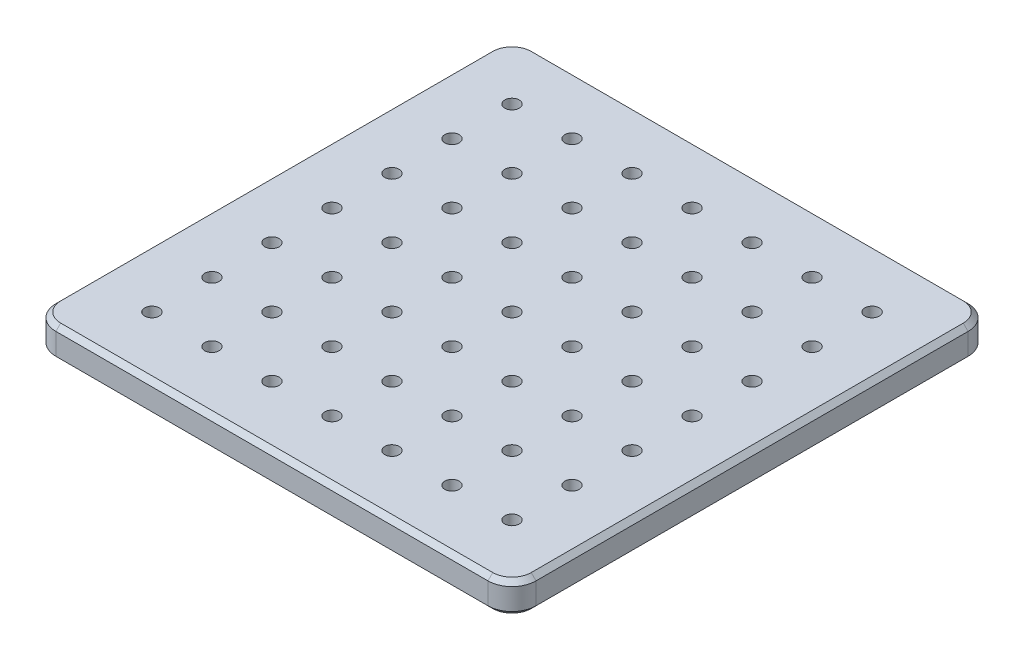
SolidWorks part; units mm, degrees
material "铸造合金钢"
ref_plane "前视基准面" through (0, 0, 0) normal (0, 0, 1) x (1, 0, 0)
ref_plane "上视基准面" through (0, 0, 0) normal (0, 1, 0) x (1, 0, 0)
ref_plane "右视基准面" through (0, 0, 0) normal (1, 0, 0) x (0, 0, -1)
sketch "草图1" plane through (0, 0, 0) normal (0, 1, 0) x (1, 0, 0)
  line L1 (-90, 100) -> (90, 100)
  line L2 (-100, 90) -> (-100, -90)
  line L3 (-90, -100) -> (90, -100)
  line L4 (100, 90) -> (100, -90)
  line L5 (-100, 100) -> (100, -100) construction
  line L6 (-100, -100) -> (100, 100) construction
  arc A0 (-90, 100) -> (-100, 90) centre (-90, 90) ccw
  arc A1 (90, 100) -> (100, 90) centre (90, 90) cw
  arc A2 (90, -100) -> (100, -90) centre (90, -90) ccw
  arc A3 (-100, -90) -> (-90, -100) centre (-90, -90) ccw
  circle A4 centre (-75, 75) radius 3
  circle A5 centre (-50, 75) radius 3
  circle A6 centre (-25, 75) radius 3
  circle A7 centre (0, 75) radius 3
  circle A8 centre (25, 75) radius 3
  circle A9 centre (50, 75) radius 3
  circle A10 centre (75, 75) radius 3
  circle A19 centre (75, 50) radius 3
  circle A20 centre (50, 50) radius 3
  circle A21 centre (25, 50) radius 3
  circle A22 centre (0, 50) radius 3
  circle A23 centre (-25, 50) radius 3
  circle A24 centre (-50, 50) radius 3
  circle A25 centre (-75, 50) radius 3
  circle A30 centre (75, 25) radius 3
  circle A31 centre (50, 25) radius 3
  circle A32 centre (25, 25) radius 3
  circle A33 centre (0, 25) radius 3
  circle A34 centre (-25, 25) radius 3
  circle A35 centre (-50, 25) radius 3
  circle A36 centre (-75, 25) radius 3
  circle A41 centre (75, 0) radius 3
  circle A42 centre (50, 0) radius 3
  circle A43 centre (25, 0) radius 3
  circle A44 centre (0, 0) radius 3
  circle A45 centre (-25, 0) radius 3
  circle A46 centre (-50, 0) radius 3
  circle A47 centre (-75, 0) radius 3
  circle A52 centre (75, -25) radius 3
  circle A53 centre (50, -25) radius 3
  circle A54 centre (25, -25) radius 3
  circle A55 centre (0, -25) radius 3
  circle A56 centre (-25, -25) radius 3
  circle A57 centre (-50, -25) radius 3
  circle A58 centre (-75, -25) radius 3
  circle A63 centre (75, -50) radius 3
  circle A64 centre (50, -50) radius 3
  circle A65 centre (25, -50) radius 3
  circle A66 centre (0, -50) radius 3
  circle A67 centre (-25, -50) radius 3
  circle A68 centre (-50, -50) radius 3
  circle A69 centre (-75, -50) radius 3
  circle A74 centre (75, -75) radius 3
  circle A75 centre (50, -75) radius 3
  circle A76 centre (25, -75) radius 3
  circle A77 centre (0, -75) radius 3
  circle A78 centre (-25, -75) radius 3
  circle A79 centre (-50, -75) radius 3
  circle A80 centre (-75, -75) radius 3
  circle A125 centre (100, 75) radius 3 [skipped]
  circle A126 centre (125, 75) radius 3 [skipped]
  circle A127 centre (150, 75) radius 3 [skipped]
  circle A128 centre (175, 75) radius 3 [skipped]
  circle A129 centre (75, -100) radius 3 [skipped]
  circle A130 centre (50, -100) radius 3 [skipped]
  circle A131 centre (25, -100) radius 3 [skipped]
  circle A132 centre (0, -100) radius 3 [skipped]
  circle A133 centre (-25, -100) radius 3 [skipped]
  circle A134 centre (-50, -100) radius 3 [skipped]
  circle A135 centre (-75, -100) radius 3 [skipped]
  circle A136 centre (75, -125) radius 3 [skipped]
  circle A137 centre (50, -125) radius 3 [skipped]
  circle A138 centre (25, -125) radius 3 [skipped]
  circle A139 centre (0, -125) radius 3 [skipped]
  circle A140 centre (-25, -125) radius 3 [skipped]
  circle A141 centre (-50, -125) radius 3 [skipped]
  circle A142 centre (-75, -125) radius 3 [skipped]
  circle A143 centre (75, -150) radius 3 [skipped]
  circle A144 centre (50, -150) radius 3 [skipped]
  circle A145 centre (25, -150) radius 3 [skipped]
  circle A146 centre (0, -150) radius 3 [skipped]
  circle A147 centre (-25, -150) radius 3 [skipped]
  circle A148 centre (-50, -150) radius 3 [skipped]
  circle A149 centre (-75, -150) radius 3 [skipped]
  circle A150 centre (75, -175) radius 3 [skipped]
  circle A151 centre (50, -175) radius 3 [skipped]
  circle A152 centre (25, -175) radius 3 [skipped]
  circle A153 centre (0, -175) radius 3 [skipped]
  circle A154 centre (-25, -175) radius 3 [skipped]
  circle A155 centre (-50, -175) radius 3 [skipped]
  circle A156 centre (-75, -175) radius 3 [skipped]
  point P0 (0, 0)
  dimension "D2" = 10
  dimension "D4" = 6
  dimension "D5" = 25
  dimension "D6" = 25
  dimension "D7" = 11
  dimension "D8" = 11
extrude "凸台-拉伸1" add sketch "草图1" along normal blind 13
chamfer "倒角1" distance 2 angle 45 16 edges at (0, 0, -100) (-97.0711, 0, -97.0711) (97.0711, 0, -97.0711) (-100, 0, 0) (100, 0, 0) (-97.0711, 0, 97.0711) (97.0711, 0, 97.0711) (0, 0, 100) (0, 13, -100) (-97.0711, 13, -97.0711) (97.0711, 13, -97.0711) (-100, 13, 0) (100, 13, 0) (-97.0711, 13, 97.0711) (97.0711, 13, 97.0711) (0, 13, 100)
